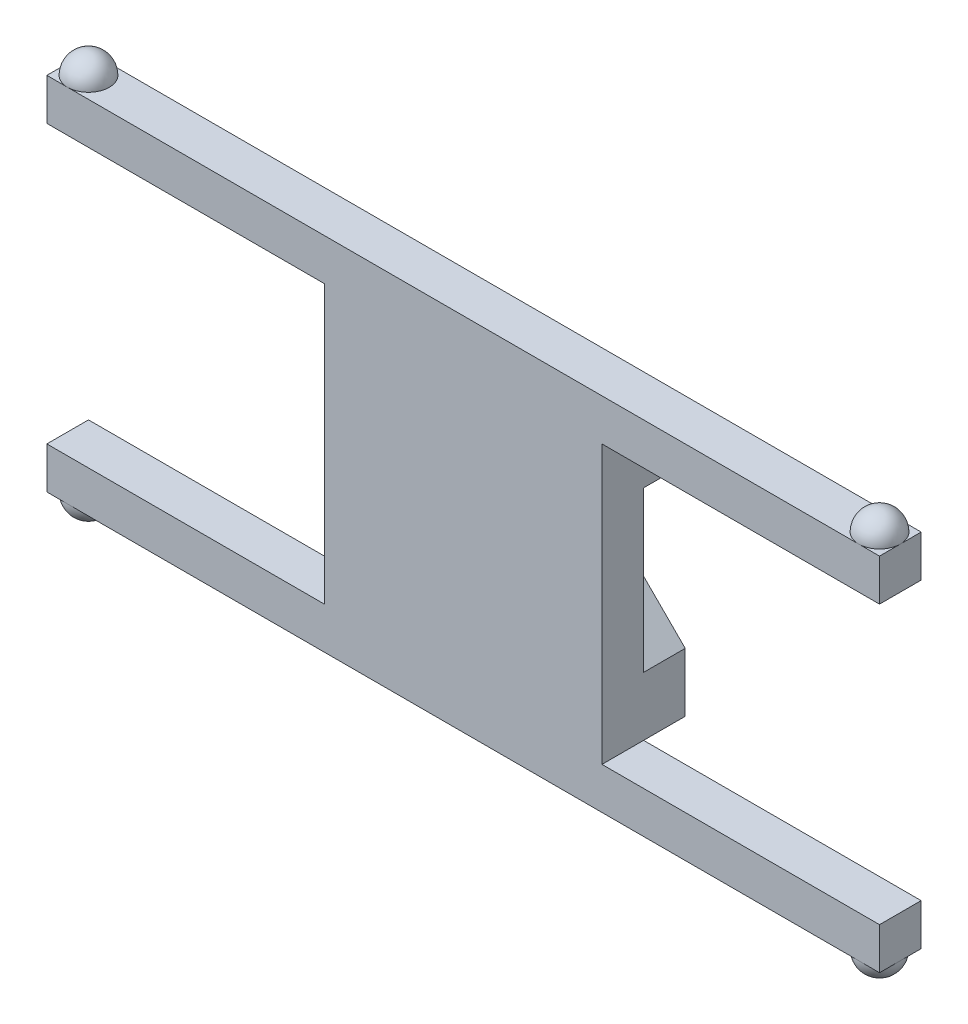
SolidWorks part; units mm, degrees
ref_plane "Front Plane" through (0, 0, 0) normal (0, 0, 1) x (1, 0, 0)
ref_plane "Top Plane" through (0, 0, 0) normal (0, 1, 0) x (1, 0, 0)
ref_plane "Right Plane" through (0, 0, 0) normal (1, 0, 0) x (0, 0, -1)
sketch "Sketch1" plane through (0, 0, 0) normal (0, 0, 1) x (1, 0, 0)
  line L0 (10, 0) -> (30, 0)
  line L1 (0, -1000) -> (0, 49000) construction
  line L2 (0, 0) -> (0, 3)
  line L3 (-27, 3) -> (27, 3)
  line L4 (0, 0) -> (0, -20)
  line L5 (-30, -23) -> (-27, -23) construction
  line L6 (30, 3) -> (30, 0)
  line L7 (10, -10) -> (49000, -10) construction
  line L8 (10, 0) -> (10, -20)
  line L9 (0, 0) -> (0, -10) construction
  line L10 (-1000, -10) -> (0, -10) construction
  line L11 (30, -23) -> (27, -23) construction
  line L12 (-10, -20) -> (-30, -20)
  line L13 (30, -23) -> (30, -20)
  line L14 (-27, -23) -> (27, -23)
  line L15 (-30, -23) -> (-30, -20)
  line L16 (0, -20) -> (0, -23)
  line L17 (10, -20) -> (30, -20)
  line L18 (-10, 0) -> (-10, -20)
  line L19 (-30, 3) -> (-30, 0)
  line L20 (-10, 0) -> (-30, 0)
  line L21 (27, 3) -> (30, 3)
  line L22 (-27, 3) -> (-30, 3)
  line L23 (-30, -23) -> (-27, -23)
  line L24 (27, -23) -> (30, -23)
  dimension "D1" = 30
  dimension "D2" = 3
  dimension "D3" = 10
  dimension "D4" = 20
  dimension "D5" = 3
  dimension "D6" = 10
  dimension "D7" = 30
  dimension "D8" = 3
  dimension "D10" = 27
  dimension "D11" = 10
  dimension "D12" = 27
extrude "Boss-Extrude1" add sketch "Sketch1" along normal blind 3 contours L3 L21 L6 L0 L8 L17 L13 L24 L14 L23 L15 L12 L18 L20 L19 L22
sketch "ball1" plane through (0, 3, 0) normal (0, 1, 0) x (1, 0, 0)
  line L0 (30, -1.5) -> (28.5, -1.5) construction
  line L1 (30, -3) -> (30, 0) construction
  line L2 (0, -3) -> (0, 0) construction
  line L3 (30, -3) -> (-30, -3) construction
  line L4 (-30, 0) -> (30, 0) construction
  line L5 (28.5, -1.5) -> (27, -1.5) construction
  line L6 (30, -1.5) -> (27, -1.5)
  line L7 (30, -1.5) -> (13.0663, -1.5) construction
  arc A0 (30, -1.5) -> (27, -1.5) centre (28.5, -1.5) ccw
  dimension "D1" = 1.5
revolve "ball1_revolved" add sketch "ball1" angle 180 about L7
sketch "ball2" plane through (0, 3, 0) normal (0, 1, 0) x (1, 0, 0)
  line L0 (-30, -1.5) -> (-27, -1.5)
  line L1 (-30, -1.5) -> (30, -1.5) construction
  line L2 (-30, -3) -> (-30, 0) construction
  arc A0 (28.5, -3) -> (30, -1.5) centre (28.5, -1.5) ccw construction
  arc A1 (-30, -1.5) -> (-27, -1.5) centre (-28.5, -1.5) ccw
  dimension "D1" = 1.5
sketch "Sketch5" plane through (0, -23, 0) normal (0, -1, 0) x (1, 0, 0)
  line L0 (-30, 1.5) -> (30, 1.5) construction
  line L1 (-30, 3) -> (-30, 0) construction
  arc A2 (-30, 1.5) -> (-27, 1.5) centre (-28.5, 1.5) cw
  arc A10 (28.5, 3) -> (28.5, 0) centre (28.5, 1.5) ccw construction
  arc A11 (30, 1.5) -> (28.5, 3) centre (28.5, 1.5) ccw construction
  arc A16 (28.5, 3) -> (27, 1.5) centre (28.5, 1.5) ccw
  arc A17 (30, 1.5) -> (28.5, 3) centre (28.5, 1.5) ccw
  dimension "D1" = 1.5
sketch "Sketch7" plane through (0, 0, 0) normal (0, 0, -1) x (-1, 0, 0)
  line L0 (-10, 0) -> (10, 0)
  line L1 (10, 0) -> (10, -20)
  line L2 (10, -20) -> (-10, -20)
  line L3 (-10, -20) -> (-10, 0)
  line L4 (10, 0) -> (-10, -20)
  line L5 (-10, 0) -> (10, -20)
  line L6 (-12.1213, -2.1213) -> (7.8787, -22.1213)
  line L7 (7.8787, 2.1213) -> (-12.1213, -17.8787)
  line L8 (-7.8787, 2.1213) -> (12.1213, -17.8787)
  line L9 (12.1213, -2.1213) -> (-7.8787, -22.1213)
  dimension "D3" = 20
  dimension "D4" = 20
  dimension "D1" = 3
  dimension "D2" = 3
sketch "Sketch8" plane through (0, 0, 0) normal (0, 0, -1) x (-1, 0, 0)
  line L0 (-10, 0) -> (10, 0) construction
  line L6 (10, -20) -> (-10, -20) construction
  line L7 (-10, -20) -> (-10, 0) construction
  line L8 (-10, 0) -> (-5.7574, 0)
  line L9 (-5.7574, 0) -> (10, -15.7574)
  line L10 (5.7574, 0) -> (-10, -15.7574)
  line L11 (10, -4.2426) -> (-5.7574, -20)
  line L12 (-10, -4.2426) -> (5.7574, -20)
  line L13 (10, 0) -> (10, -4.2426)
  line L14 (10, -20) -> (5.7574, -20)
  line L15 (-10, -20) -> (-10, -15.7574)
  line L16 (-10, 0) -> (10, -20) construction
  line L17 (-10, 0) -> (-7.8787, -2.1213) construction
  line L18 (-7.8787, -2.1213) -> (-5.7574, 0) construction
  line L19 (5.7574, 0) -> (10, 0)
  line L20 (10, -20) -> (7.8787, -17.8787) construction
  line L21 (7.8787, -17.8787) -> (10, -15.7574) construction
  line L22 (10, -15.7574) -> (10, -20)
  line L24 (10, 0) -> (-10, -20) construction
  line L25 (10, 0) -> (7.8787, -2.1213) construction
  line L26 (7.8787, -2.1213) -> (10, -4.2426) construction
  line L27 (7.8787, -2.1213) -> (5.7574, 0) construction
  line L28 (-10, -20) -> (-7.8787, -17.8787) construction
  line L29 (-7.8787, -17.8787) -> (-5.7574, -20) construction
  line L30 (-7.8787, -17.8787) -> (-10, -15.7574) construction
  line L31 (-10, -4.2426) -> (-10, 0)
  line L32 (-5.7574, -20) -> (-10, -20)
  line L33 (-7.8787, -2.1213) -> (-10, -4.2426) construction
  line L34 (-10, 0) -> (-10, -20) construction
  line L35 (7.8787, -17.8787) -> (5.7574, -20) construction
  line M7 (-10, 0) -> (-10, -20)
  line M15 (10, -20) -> (10, 0)
  dimension "D1" = 3
  dimension "D2" = 3
  dimension "D3" = 3
  dimension "D4" = 3
  dimension "D5" = 3
  dimension "D6" = 3
  dimension "D7" = 3
  dimension "D8" = 3
  dimension "D9" = 3
  dimension "D10" = 3
extrude "Boss-Extrude3" add sketch "Sketch8" along normal blind 3 contours L12 L10 L9 L8 M7 | L19 L10 L9 L11 M15 | L10 L12 L11 L9 | L14 L9 L11 L12 M15 | L32 L11 L12 L10 M7
revolve "Revolve4" add sketch "Sketch5" angle 360 about L0
revolve "Revolve5" add sketch "ball2" angle 360 about L1
